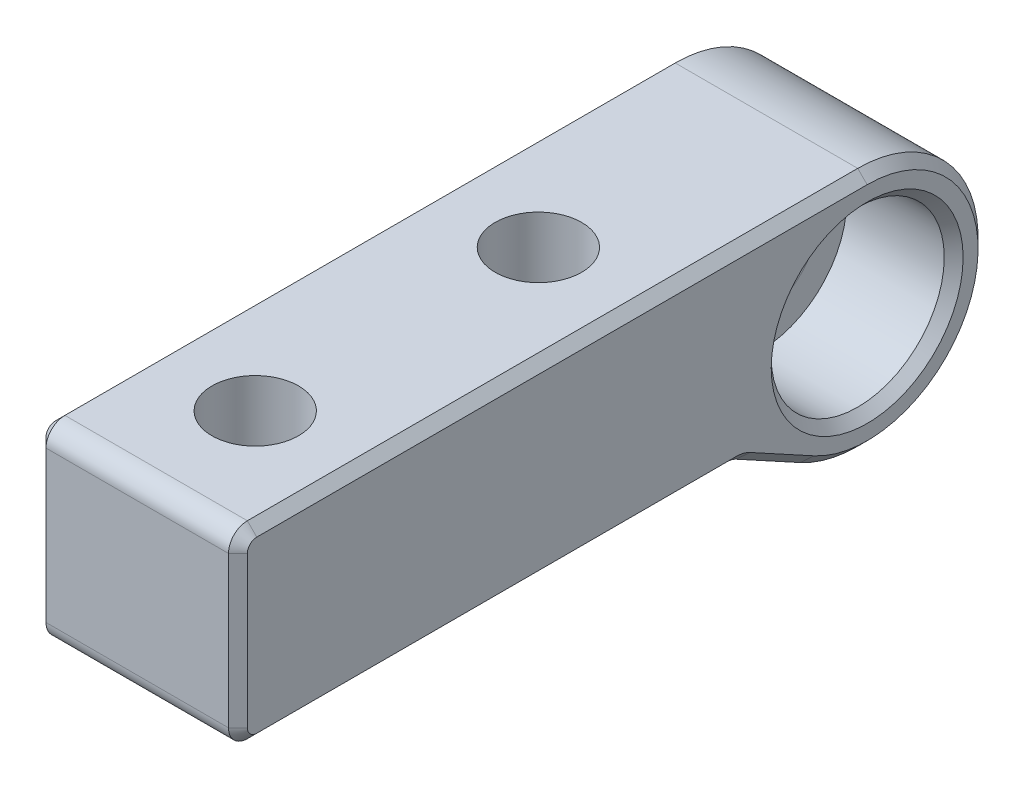
SolidWorks part; units mm, degrees
ref_plane "Front Plane" through (0, 0, 0) normal (0, 0, 1) x (1, 0, 0)
ref_plane "Top Plane" through (0, 0, 0) normal (0, 1, 0) x (1, 0, 0)
ref_plane "Right Plane" through (0, 0, 0) normal (1, 0, 0) x (0, 0, -1)
sketch "Sketch5" plane through (0, 0, 0) normal (1, 0, 0) x (0, -1, 0)
  line L0 (-7.65, 0) -> (-7.65, -40)
  line L3 (0, 0) -> (0, -40) construction
  line L7 (4.35, -8) -> (6.7157, -3.6637)
  line L8 (4.35, -8) -> (4.35, -40)
  line L9 (4.35, -40) -> (-7.65, -40)
  circle A0 centre (0, 0) radius 3.15
  arc A1 (7.65, 0) -> (-7.65, 0) centre (0, 0) ccw
  circle A2 centre (0, 0) radius 7.65 construction
  arc A3 (7.65, 0) -> (6.7157, -3.6637) centre (0, 0) cw
  dimension "D1" = 6.3
  dimension "D3" = 40
  dimension "D4" = 12
  dimension "D5" = 32
  dimension "D2" = 4.5
extrude "Boss-Extrude5" add sketch "Sketch5" along normal blind 12.8
hole_wizard "CBORE for M5 Hex Head Bolt1" positions "Sketch6" profile "Sketch7" counterbore size "M5" standard "ANSI Metric" end condition through all
sketch "Sketch6" plane through (0, -4.35, 0) normal (0, -1, 0) x (-1, 0, 0)
  line L0 (-6.4, -32.5) -> (-6.4, -14.5) construction
  line L1 (-6.4, -32.5) -> (-6.4, -40) construction
  line L3 (-12.8, -40) -> (0, -40) construction
  point P0 (-6.4, -14.5)
  point P2 (-6.4, -32.5)
  dimension "D1" = 18
  dimension "D2" = 7.5
sketch "Sketch7" plane through (6.4, -4.35, 14.5) normal (1, 0, 0) x (0, 0, -1)
  line L0 (0, 0) -> (0, 12)
  line L1 (0, 12) -> (2.75, 12)
  line L3 (2.75, 12) -> (2.75, 5.5)
  line L4 (2.75, 5.5) -> (5, 5.5)
  line L5 (5, 5.5) -> (5, 0)
  line L7 (5, 0) -> (0, 0)
  line L11 (0, -6.35) -> (0, 107.95) construction
  dimension "Thru Hole Dia." = 5.5
  dimension "Thru Hole Depth" = 12
  dimension "C'Bore Dia." = 10
  dimension "C'Bore Depth" = 5.5
sketch "Sketch8" plane through (12.8, 0, 0) normal (1, 0, 0) x (0, 0, -1)
  circle A0 centre (0, 0) radius 5.5
  dimension "D1" = 11
extrude "Cut-Extrude-LEFT" cut sketch "Sketch8" against normal offset from surface (6.8 mm away) 6 up to face at (0, -0.4947, 16.4838)
sketch "Sketch9" [suppressed] plane through (0, 0, 0) normal (-1, 0, 0) x (0, 0, 1)
  circle A0 centre (0, 0) radius 5.5
  dimension "D1" = 11
extrude "Cut-Extrude-RIGHT" [suppressed] cut sketch "Sketch9" against normal offset from surface (6.8 mm away) 6
fillet "Fillet5" radius 1.2 3 edges at (6.4, 7.65, 40) (6.4, -4.35, 40) (6.4, -4.35, 8)
chamfer "Chamfer2" distance 0.6 angle 45 18 edges at (0, 0, -3.15) (0, 7.65, 19.4) (0, -1.8905, -7.4127) (12.8, 7.65, 19.4) (12.8, -1.8905, -7.4127) (0, -5.6061, 5.6975) (0, 1.65, 40) (0, -4.35, 23.553) (12.8, 1.65, 40) (12.8, -5.6061, 5.6975) (12.8, -4.35, 23.553) (0, -3.9985, 39.6485) (0, 7.2985, 39.6485) (12.8, -3.9985, 39.6485) (12.8, 7.2985, 39.6485) (0, -4.3872, 8.0095) (12.8, -4.3872, 8.0095) (12.8, 0, -5.5)
fillet "Fillet6" [suppressed] radius 0.5
fillet "Fillet7" radius 0.5 1 edges at (6, 0, -3.15)
equation "\"D5@Sketch5\"=\"D3@Sketch5\"-8"
